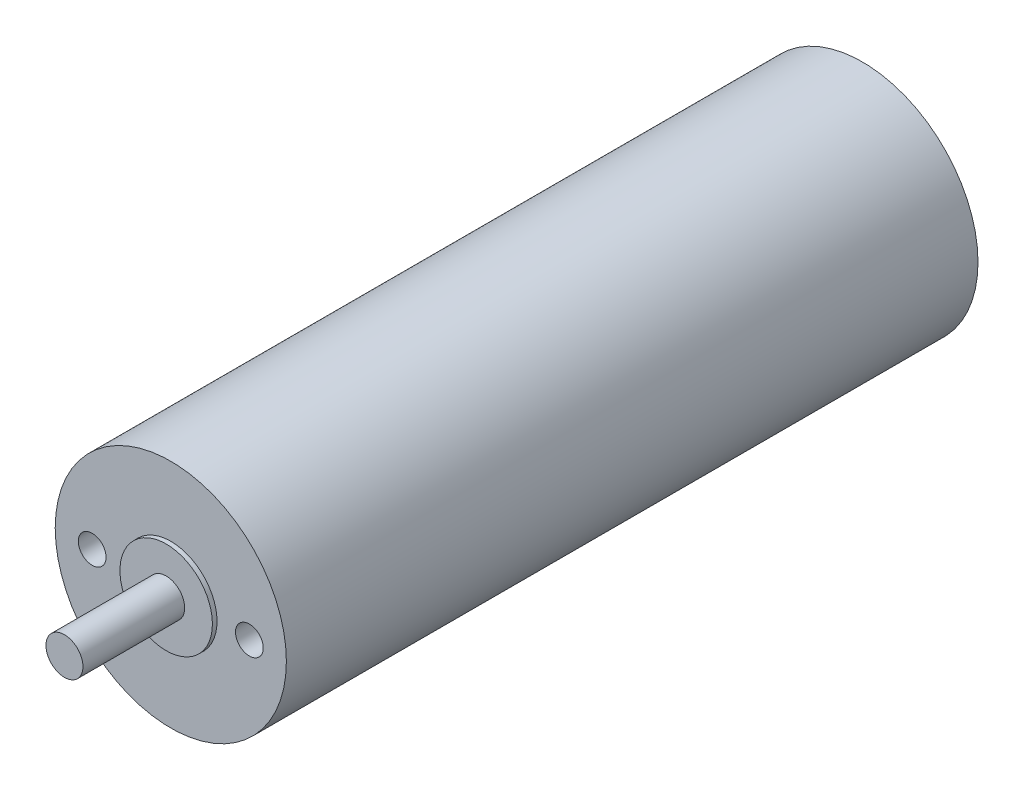
SolidWorks part; units mm, degrees
ref_plane "Front Plane" through (0, 0, 0) normal (0, 0, 1) x (1, 0, 0)
ref_plane "Top Plane" through (0, 0, 0) normal (0, 1, 0) x (1, 0, 0)
ref_plane "Right Plane" through (0, 0, 0) normal (1, 0, 0) x (0, 0, -1)
sketch "Sketch3" plane through (0, 0, 0) normal (0, 0, 1) x (1, 0, 0)
  circle A2 centre (0, 0) radius 12.5
  dimension "D1" = 25
extrude "Boss-Extrude1" add sketch "Sketch3" along normal blind 74.8 contours A2
sketch "Sketch4" plane through (0, 0, 74.8) normal (0, 0, 1) x (1, 0, 0)
  circle A0 centre (0, 0) radius 5
  dimension "D1" = 10
extrude "Boss-Extrude2" add sketch "Sketch4" along normal blind 0.5
sketch "Sketch5" plane through (0, 0, 75.3) normal (0, 0, 1) x (1, 0, 0)
  circle A0 centre (0, 0) radius 2
  dimension "D1" = 4
extrude "Boss-Extrude3" add sketch "Sketch5" along normal blind 11
sketch "Sketch6" plane through (0, 0, 74.8) normal (0, 0, 1) x (1, 0, 0)
  line L0 (-8.5, 0) -> (8.5, 0) construction
  circle A0 centre (-8.5, 0) radius 1.5
  circle A1 centre (8.5, 0) radius 1.5
  point P4 (0, 0)
  dimension "D1" = 17
  dimension "D2" = 3
extrude "Cut-Extrude1" cut sketch "Sketch6" against normal blind 4
